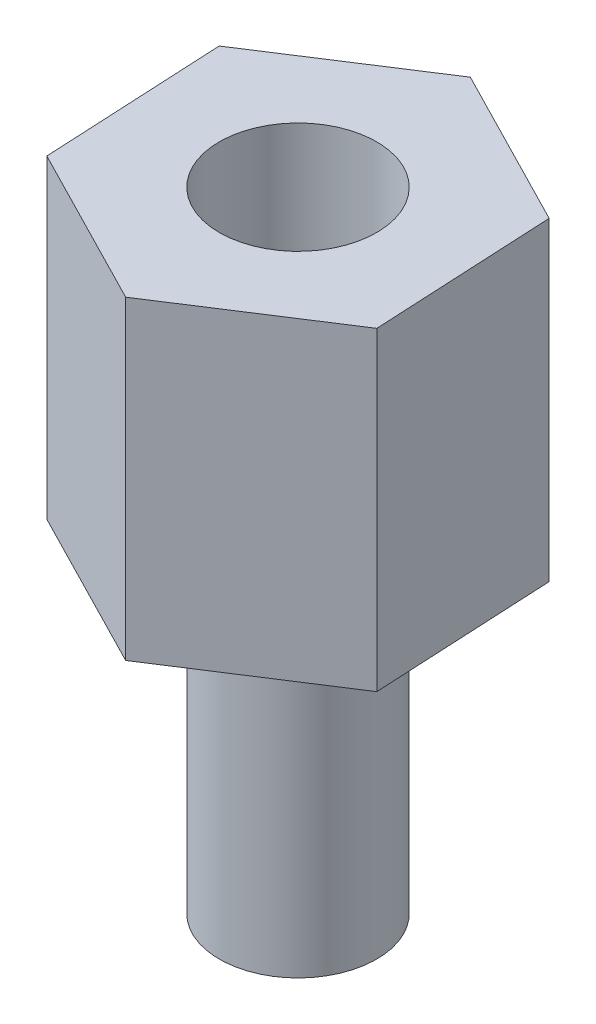
SolidWorks part; units mm, degrees
ref_plane "Plan de face" through (0, 0, 0) normal (0, 0, 1) x (1, 0, 0)
ref_plane "Plan de dessus" through (0, 0, 0) normal (0, 1, 0) x (1, 0, 0)
ref_plane "Plan de droite" through (0, 0, 0) normal (1, 0, 0) x (0, 0, -1)
sketch "Esquisse1" plane through (0, 0, 0) normal (0, 1, 0) x (1, 0, 0)
  line L1 (2.4246, 1.5667) -> (-0.1445, 2.8831)
  line L2 (-0.1445, 2.8831) -> (-2.5691, 1.3164)
  line L3 (-2.5691, 1.3164) -> (-2.4246, -1.5667)
  line L4 (-2.4246, -1.5667) -> (0.1445, -2.8831)
  line L5 (0.1445, -2.8831) -> (2.5691, -1.3164)
  line L6 (2.5691, -1.3164) -> (2.4246, 1.5667)
  circle A0 centre (0, 0) radius 2.5 construction
extrude "Extrusion1" add sketch "Esquisse1" along normal blind 5
sketch "Esquisse2" plane through (0, 0, 0) normal (0, -1, 0) x (1, 0, 0)
  circle A0 centre (0, 0) radius 1.25
extrude "Extrusion2" add sketch "Esquisse2" along normal blind 5
sketch "Esquisse3" plane through (0, 5, 0) normal (0, 1, 0) x (-1, 0, 0)
  circle A0 centre (0, 0) radius 1.25
extrude "Enlèv. mat.-Extru.2" cut sketch "Esquisse3" against normal blind 4
